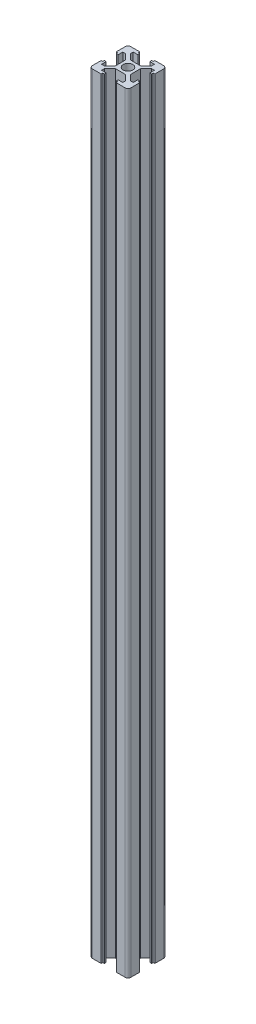
SolidWorks part; units mm, degrees
material "6063-O"
ref_plane "Front Plane" through (0, 0, 0) normal (0, 0, 1) x (1, 0, 0)
ref_plane "Top Plane" through (0, 0, 0) normal (0, 1, 0) x (1, 0, 0)
ref_plane "Right Plane" through (0, 0, 0) normal (1, 0, 0) x (0, 0, -1)
sketch "Sketch1" plane through (0, 0, 0) normal (0, 1, 0) x (1, 0, 0)
  line L0 (0, 14.5399) -> (0, 10) construction
  line L1 (-16.8658, 0) -> (2.5, 0) construction
  line L2 (13.2784, 3.9) -> (3.9, 3.9) construction
  line L3 (0, 0) -> (2.5, 0)
  line L4 (0, 0) -> (0, 2.5)
  line L5 (3.9, 10) -> (8.5, 10)
  line L6 (9.2, 0) -> (16.4291, 0) construction
  line L7 (-2.63, 3.9) -> (2.63, 3.9)
  line L9 (2.5491, 3.9) -> (2.63, 3.9)
  line L10 (3.9, 0) -> (3.9, 2.63)
  line L11 (13.2784, 3.1) -> (2.5491, 3.1) construction
  line L12 (8.2, 7.5573) -> (8.2, -3.0868) construction
  line L13 (9.2, 7.2593) -> (9.2, -8.1534) construction
  line L14 (10, 3.9) -> (9.2, 3.9)
  line L15 (9.2, 3.9) -> (9.2, 3.1)
  line L16 (9.2, 3.1) -> (8.2, 3.1)
  line L17 (8.2, 3.1) -> (8.2, 5.5)
  line L18 (8.2, 5.5) -> (6.77, 5.5)
  line L19 (6.77, 5.5) -> (3.9, 2.63)
  line L20 (5.0973, 5.5) -> (13.0082, 5.5) construction
  line L21 (3.1, 11.2046) -> (3.1, 2.6994) construction
  line L22 (3.9, 10.7498) -> (3.9, 3.9) construction
  line L23 (5.5, 11.523) -> (5.5, 1.4941) construction
  line L24 (-2.2597, 8.2) -> (6.1545, 8.2) construction
  line L25 (-2.9419, 9.2) -> (5.7225, 9.2) construction
  line L26 (3.9, 10) -> (3.9, 9.2)
  line L27 (3.9, 9.2) -> (3.1, 9.2)
  line L28 (3.1, 9.2) -> (3.1, 8.2)
  line L29 (3.1, 8.2) -> (5.5, 8.2)
  line L30 (5.5, 8.2) -> (5.5, 6.77)
  line L31 (5.5, 6.77) -> (2.63, 3.9)
  line L32 (0, 2.5) -> (0, -14.4122) construction
  line L33 (10, 3.9) -> (10, 8.5)
  line L34 (9.2, 0) -> (10, 0)
  line L35 (2.63, 3.9) -> (2.5491, 3.9) construction
  line L36 (3.9, 2.63) -> (3.9, 2.0627) construction
  line L37 (10, -3.9) -> (10, -8.5)
  line L38 (3.9, -10) -> (8.5, -10)
  line L39 (3.9, -10) -> (3.9, -9.2)
  line L40 (3.9, -9.2) -> (3.1, -9.2)
  line L41 (3.1, -9.2) -> (3.1, -8.2)
  line L42 (3.1, -8.2) -> (5.5, -8.2)
  line L43 (5.5, -8.2) -> (5.5, -6.77)
  line L44 (5.5, -6.77) -> (2.63, -3.9)
  line L45 (0, -3.9) -> (2.63, -3.9)
  line L46 (3.9, 0) -> (3.9, -2.63)
  line L47 (6.77, -5.5) -> (3.9, -2.63)
  line L48 (8.2, -5.5) -> (6.77, -5.5)
  line L49 (8.2, -3.1) -> (8.2, -5.5)
  line L50 (9.2, -3.1) -> (8.2, -3.1)
  line L51 (9.2, -3.9) -> (9.2, -3.1)
  line L52 (10, -3.9) -> (9.2, -3.9)
  line L53 (-3.9, -10) -> (-8.5, -10)
  line L54 (-10, -3.9) -> (-10, -8.5)
  line L55 (-10, -3.9) -> (-9.2, -3.9)
  line L56 (-9.2, -3.9) -> (-9.2, -3.1)
  line L57 (-9.2, -3.1) -> (-8.2, -3.1)
  line L58 (-8.2, -3.1) -> (-8.2, -5.5)
  line L59 (-8.2, -5.5) -> (-6.77, -5.5)
  line L60 (-6.77, -5.5) -> (-3.9, -2.63)
  line L61 (-3.9, 0) -> (-3.9, -2.63)
  line L62 (0, -3.9) -> (-2.63, -3.9)
  line L63 (-5.5, -6.77) -> (-2.63, -3.9)
  line L64 (-5.5, -8.2) -> (-5.5, -6.77)
  line L65 (-3.1, -8.2) -> (-5.5, -8.2)
  line L66 (-3.1, -9.2) -> (-3.1, -8.2)
  line L67 (-3.9, -9.2) -> (-3.1, -9.2)
  line L68 (-3.9, -10) -> (-3.9, -9.2)
  line L69 (-10, 3.9) -> (-10, 8.5)
  line L70 (-3.9, 10) -> (-8.5, 10)
  line L71 (-3.9, 10) -> (-3.9, 9.2)
  line L72 (-3.9, 9.2) -> (-3.1, 9.2)
  line L73 (-3.1, 9.2) -> (-3.1, 8.2)
  line L74 (-3.1, 8.2) -> (-5.5, 8.2)
  line L75 (-5.5, 8.2) -> (-5.5, 6.77)
  line L76 (-5.5, 6.77) -> (-2.63, 3.9)
  line L78 (-3.9, 0) -> (-3.9, 2.63)
  line L79 (-6.77, 5.5) -> (-3.9, 2.63)
  line L80 (-8.2, 5.5) -> (-6.77, 5.5)
  line L81 (-8.2, 3.1) -> (-8.2, 5.5)
  line L82 (-9.2, 3.1) -> (-8.2, 3.1)
  line L83 (-9.2, 3.9) -> (-9.2, 3.1)
  line L84 (-10, 3.9) -> (-9.2, 3.9)
  line L85 (0, 3.9) -> (-2.63, 3.9) [skipped]
  circle A0 centre (0, 0) radius 2.5
  arc A1 (8.5, 10) -> (10, 8.5) centre (8.5, 8.5) cw
  arc A2 (10, -8.5) -> (8.5, -10) centre (8.5, -8.5) cw
  arc A4 (-8.5, -10) -> (-10, -8.5) centre (-8.5, -8.5) cw
  arc A6 (-10, 8.5) -> (-8.5, 10) centre (-8.5, 8.5) cw
  point P12 (10, 10)
  point P126 (0, 0)
  dimension "D3" = 5
  dimension "D4" = 1.5
  dimension "D1" = 10
  dimension "D2" = 10
  dimension "D6" = 3.9
  dimension "D7" = 3.9
  dimension "D8" = 3.1
  dimension "D9" = 4
  dimension "D11" = 5.5
  dimension "D12" = 1.8
  dimension "D13" = 0.8
  dimension "D14" = 3.9
  dimension "D15" = 3.1
  dimension "D16" = 5.5
  dimension "D17" = 1.27
  dimension "D18" = 1.27
  dimension "D19" = 1.27
  dimension "D20" = 1.27
extrude "Boss-Extrude1" add sketch "Sketch1" along normal blind 400 contours A6 L69 L84 L83 L82 L81 L80 L79 L78 L61 L60 L59 L58 L57 L56 L55 L54 A4 L53 L68 L67 L66 L65 L64 L63 L62 L45 L44 L43 L42 L41 L40 L39 L38 A2 L37 L52 L51 L50 L49 L48 L47 L46 L10 L19 L18 L17 L16 L15 L14 L33
